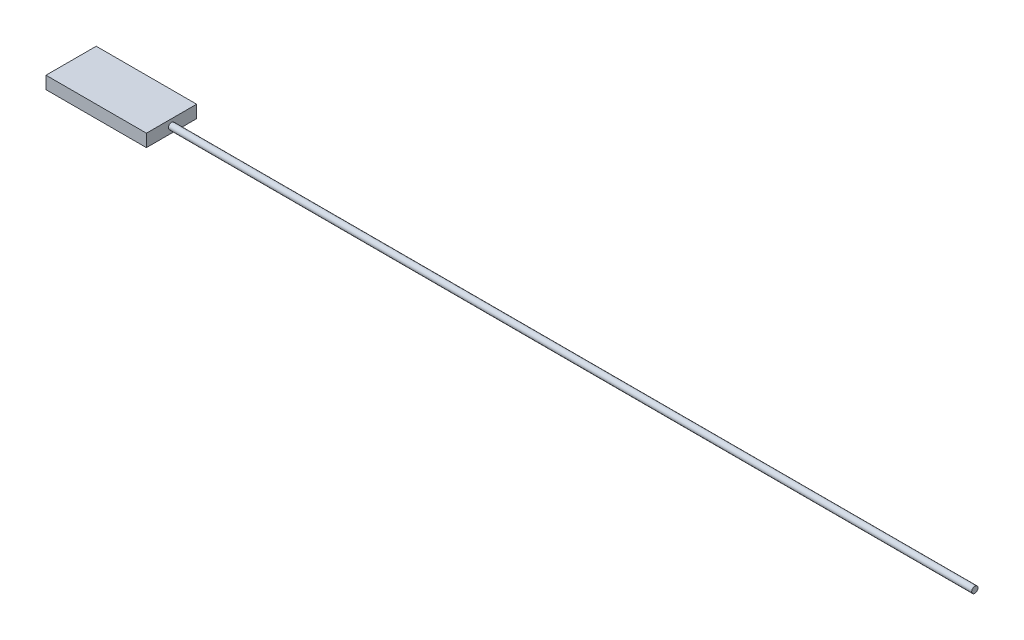
SolidWorks part; units mm, degrees
ref_plane "Front Plane" through (0, 0, 0) normal (0, 0, 1) x (1, 0, 0)
ref_plane "Top Plane" through (0, 0, 0) normal (0, 1, 0) x (1, 0, 0)
ref_plane "Right Plane" through (0, 0, 0) normal (1, 0, 0) x (0, 0, -1)
sketch "Sketch1" plane through (0, 0, 0) normal (0, 1, 0) x (1, 0, 0)
  line L1 (-25.4, -12.7) -> (25.4, -12.7)
  line L2 (-25.4, -12.7) -> (-25.4, 12.7)
  line L3 (-25.4, 12.7) -> (25.4, 12.7)
  line L4 (25.4, -12.7) -> (25.4, 12.7)
  line L5 (-25.4, -12.7) -> (25.4, 12.7) construction
  line L6 (-25.4, 12.7) -> (25.4, -12.7) construction
  point P0 (0, 0)
  dimension "D1" = 25.4
  dimension "D2" = 50.8
extrude "Boss-Extrude1" add sketch "Sketch1" along normal blind 6.35
sketch "Sketch2" plane through (25.4, 0, 0) normal (1, 0, 0) x (0, 0, -1)
  line L0 (0, 0) -> (0, 3.175) construction
  circle A0 centre (0, 3.175) radius 1.5875
  dimension "D1" = 3.175
  dimension "D2" = 3.175
extrude "Boss-Extrude2" add sketch "Sketch2" along normal blind 406.4
